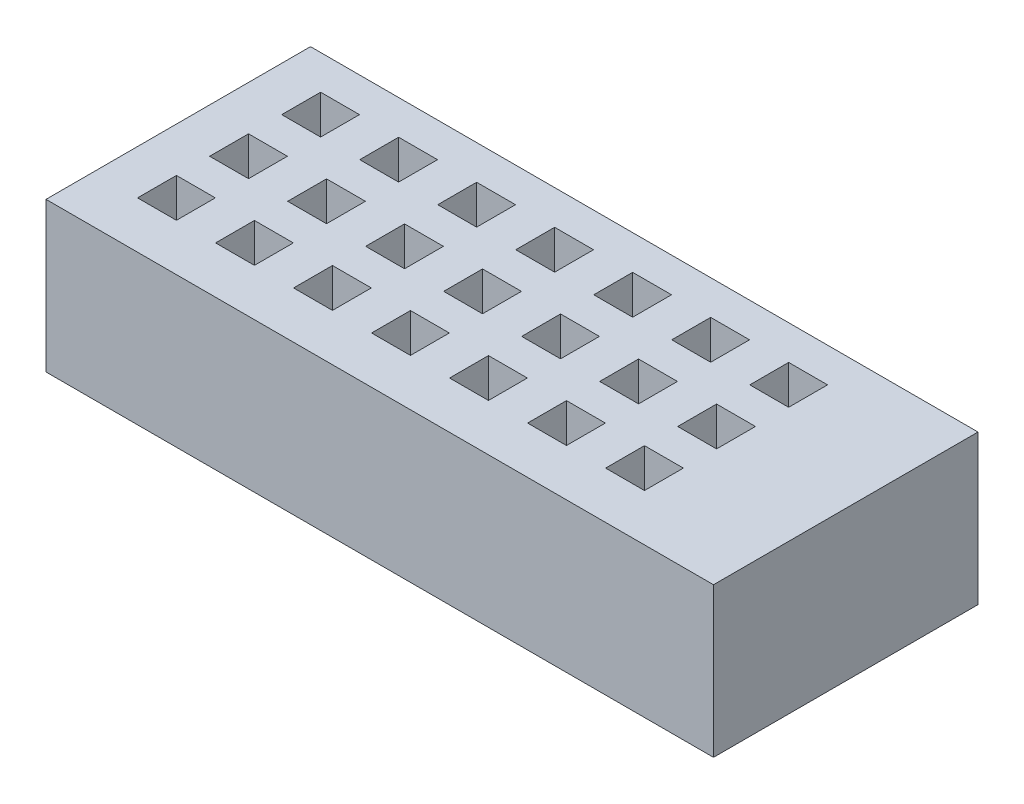
SolidWorks part; units mm, degrees
ref_plane "Front Plane" through (0, 0, 0) normal (0, 0, 1) x (1, 0, 0)
ref_plane "Top Plane" through (0, 0, 0) normal (0, 1, 0) x (1, 0, 0)
ref_plane "Right Plane" through (0, 0, 0) normal (1, 0, 0) x (0, 0, -1)
sketch "Sketch2" plane through (0, 8.128, 0) normal (0, -1, 0) x (1, 0, 0)
  line L4 (0, -10.7442) -> (-3.302, -10.7442) construction
  line L5 (-3.302, 4.064) -> (44.323, 4.064)
  line L6 (-3.302, 4.064) -> (-3.302, -14.8082)
  line L7 (-3.302, -14.8082) -> (44.323, -14.8082)
  line L8 (3.429, -0.8382) -> (3.429, 0.254)
  line L9 (3.429, 0.254) -> (-0.254, 0.254)
  line L10 (-0.254, 0.254) -> (-0.254, -0.8382)
  line L11 (-0.254, -0.8382) -> (3.429, -0.8382)
  line L12 (3.429, -0.8382) -> (3.429, 0.254)
  line L13 (3.429, 0.254) -> (-0.254, 0.254)
  line L14 (-0.254, 0.254) -> (-0.254, -0.8382)
  line L15 (-0.254, -0.8382) -> (3.429, -0.8382)
  line L16 (44.323, 4.064) -> (44.323, -14.8082)
  line L17 (0, 0) -> (0, 4.064) construction
  line L18 (41.783, 0) -> (44.323, 0) construction
  line L19 (41.783, -10.7442) -> (41.783, -14.8082) construction
  line L20 (5.2614, -0.8382) -> (8.9444, -0.8382)
  line L21 (8.9444, -0.8382) -> (8.9444, 0.254)
  line L22 (8.9444, 0.254) -> (5.2614, 0.254)
  line L23 (5.2614, 0.254) -> (5.2614, -0.8382)
  line L24 (10.7769, -0.8382) -> (14.4599, -0.8382)
  line L25 (14.4599, -0.8382) -> (14.4599, 0.254)
  line L26 (14.4599, 0.254) -> (10.7769, 0.254)
  line L27 (10.7769, 0.254) -> (10.7769, -0.8382)
  line L28 (16.2923, -0.8382) -> (19.9753, -0.8382)
  line L29 (19.9753, -0.8382) -> (19.9753, 0.254)
  line L30 (19.9753, 0.254) -> (16.2923, 0.254)
  line L31 (16.2923, 0.254) -> (16.2923, -0.8382)
  line L32 (21.8077, -0.8382) -> (25.4907, -0.8382)
  line L33 (25.4907, -0.8382) -> (25.4907, 0.254)
  line L34 (25.4907, 0.254) -> (21.8077, 0.254)
  line L35 (21.8077, 0.254) -> (21.8077, -0.8382)
  line L36 (27.3231, -0.8382) -> (31.0061, -0.8382)
  line L37 (31.0061, -0.8382) -> (31.0061, 0.254)
  line L38 (31.0061, 0.254) -> (27.3231, 0.254)
  line L39 (27.3231, 0.254) -> (27.3231, -0.8382)
  line L40 (32.8386, -0.8382) -> (36.5216, -0.8382)
  line L41 (36.5216, -0.8382) -> (36.5216, 0.254)
  line L42 (36.5216, 0.254) -> (32.8386, 0.254)
  line L43 (32.8386, 0.254) -> (32.8386, -0.8382)
  line L44 (38.354, -0.8382) -> (42.037, -0.8382)
  line L45 (42.037, -0.8382) -> (42.037, 0.254)
  line L46 (42.037, 0.254) -> (38.354, 0.254)
  line L47 (38.354, 0.254) -> (38.354, -0.8382)
  line L48 (5.2614, -5.9182) -> (8.9444, -5.9182)
  line L49 (8.9444, -5.9182) -> (8.9444, -4.826)
  line L50 (8.9444, -4.826) -> (5.2614, -4.826)
  line L51 (5.2614, -4.826) -> (5.2614, -5.9182)
  line L52 (10.7769, -5.9182) -> (14.4599, -5.9182)
  line L53 (14.4599, -5.9182) -> (14.4599, -4.826)
  line L54 (14.4599, -4.826) -> (10.7769, -4.826)
  line L55 (10.7769, -4.826) -> (10.7769, -5.9182)
  line L56 (16.2923, -5.9182) -> (19.9753, -5.9182)
  line L57 (19.9753, -5.9182) -> (19.9753, -4.826)
  line L58 (19.9753, -4.826) -> (16.2923, -4.826)
  line L59 (16.2923, -4.826) -> (16.2923, -5.9182)
  line L60 (21.8077, -5.9182) -> (25.4907, -5.9182)
  line L61 (25.4907, -5.9182) -> (25.4907, -4.826)
  line L62 (25.4907, -4.826) -> (21.8077, -4.826)
  line L63 (21.8077, -4.826) -> (21.8077, -5.9182)
  line L64 (27.3231, -5.9182) -> (31.0061, -5.9182)
  line L65 (31.0061, -5.9182) -> (31.0061, -4.826)
  line L66 (31.0061, -4.826) -> (27.3231, -4.826)
  line L67 (27.3231, -4.826) -> (27.3231, -5.9182)
  line L68 (32.8386, -5.9182) -> (36.5216, -5.9182)
  line L69 (36.5216, -5.9182) -> (36.5216, -4.826)
  line L70 (36.5216, -4.826) -> (32.8386, -4.826)
  line L71 (32.8386, -4.826) -> (32.8386, -5.9182)
  line L72 (38.354, -5.9182) -> (42.037, -5.9182)
  line L73 (42.037, -5.9182) -> (42.037, -4.826)
  line L74 (42.037, -4.826) -> (38.354, -4.826)
  line L75 (38.354, -4.826) -> (38.354, -5.9182)
  line L76 (5.2614, -10.9982) -> (8.9444, -10.9982)
  line L77 (8.9444, -10.9982) -> (8.9444, -9.906)
  line L78 (8.9444, -9.906) -> (5.2614, -9.906)
  line L79 (5.2614, -9.906) -> (5.2614, -10.9982)
  line L80 (10.7769, -10.9982) -> (14.4599, -10.9982)
  line L81 (14.4599, -10.9982) -> (14.4599, -9.906)
  line L82 (14.4599, -9.906) -> (10.7769, -9.906)
  line L83 (10.7769, -9.906) -> (10.7769, -10.9982)
  line L84 (16.2923, -10.9982) -> (19.9753, -10.9982)
  line L85 (19.9753, -10.9982) -> (19.9753, -9.906)
  line L86 (19.9753, -9.906) -> (16.2923, -9.906)
  line L87 (16.2923, -9.906) -> (16.2923, -10.9982)
  line L88 (21.8077, -10.9982) -> (25.4907, -10.9982)
  line L89 (25.4907, -10.9982) -> (25.4907, -9.906)
  line L90 (25.4907, -9.906) -> (21.8077, -9.906)
  line L91 (21.8077, -9.906) -> (21.8077, -10.9982)
  line L92 (27.3231, -10.9982) -> (31.0061, -10.9982)
  line L93 (31.0061, -10.9982) -> (31.0061, -9.906)
  line L94 (31.0061, -9.906) -> (27.3231, -9.906)
  line L95 (27.3231, -9.906) -> (27.3231, -10.9982)
  line L96 (32.8386, -10.9982) -> (36.5216, -10.9982)
  line L97 (36.5216, -10.9982) -> (36.5216, -9.906)
  line L98 (36.5216, -9.906) -> (32.8386, -9.906)
  line L99 (32.8386, -9.906) -> (32.8386, -10.9982)
  line L100 (38.354, -10.9982) -> (42.037, -10.9982)
  line L101 (42.037, -10.9982) -> (42.037, -9.906)
  line L102 (42.037, -9.906) -> (38.354, -9.906)
  line L103 (38.354, -9.906) -> (38.354, -10.9982)
  line L104 (-0.254, -5.9182) -> (3.429, -5.9182)
  line L105 (3.429, -5.9182) -> (3.429, -4.826)
  line L106 (3.429, -4.826) -> (-0.254, -4.826)
  line L107 (-0.254, -4.826) -> (-0.254, -5.9182)
  line L108 (-0.254, -10.9982) -> (3.429, -10.9982)
  line L109 (3.429, -10.9982) -> (3.429, -9.906)
  line L110 (3.429, -9.906) -> (-0.254, -9.906)
  line L111 (-0.254, -9.906) -> (-0.254, -10.9982)
  line L112 (0, -0.5842) -> (-0.254, -0.5842) construction
  line L113 (41.783, -0.5842) -> (42.037, -0.5842) construction
  dimension "D2" = 4.064
  dimension "D5" = 5.08
  dimension "D6" = 3.302
  dimension "D7" = 4.064
  dimension "D8" = 2.54
  dimension "D1" = 0.254
  dimension "D3" = 8
  dimension "D4" = 3
extrude "Boss-Extrude2" add sketch "Sketch2" along normal offset from surface (6.858 mm away) 1.27
sketch "Sketch4" plane through (0, 8.128, 0) normal (0, 1, 0) x (1, 0, 0)
  circle A1 centre (1.26, 0.6802) radius 0.731
  circle A2 centre (1.26, 0.6802) radius 0.35 construction
  circle A3 centre (6.8258, 0.6802) radius 0.731
  circle A4 centre (12.3915, 0.6802) radius 0.731
  circle A5 centre (17.9573, 0.6802) radius 0.731
  circle A6 centre (23.5231, 0.6802) radius 0.731
  circle A7 centre (29.0888, 0.6802) radius 0.731
  circle A8 centre (34.6546, 0.6802) radius 0.731
  circle A9 centre (40.2204, 0.6802) radius 0.731
  circle A10 centre (6.8258, 5.7602) radius 0.731
  circle A11 centre (12.3915, 5.7602) radius 0.731
  circle A12 centre (17.9573, 5.7602) radius 0.731
  circle A13 centre (23.5231, 5.7602) radius 0.731
  circle A14 centre (29.0888, 5.7602) radius 0.731
  circle A15 centre (34.6546, 5.7602) radius 0.731
  circle A16 centre (40.2204, 5.7602) radius 0.731
  circle A24 centre (1.26, 5.7602) radius 0.731
  circle A26 centre (1.26, 10.8402) radius 0.731
  circle A27 centre (6.8258, 10.8402) radius 0.731
  circle A28 centre (12.3915, 10.8402) radius 0.731
  circle A29 centre (17.9573, 10.8402) radius 0.731
  circle A30 centre (23.5231, 10.8402) radius 0.731
  circle A31 centre (29.0888, 10.8402) radius 0.731
  circle A32 centre (34.6546, 10.8402) radius 0.731
  circle A33 centre (40.2204, 10.8402) radius 0.731
  dimension "D1" = 0.381
  dimension "D4" = 5.08
  dimension "D2" = 8
  dimension "D3" = 3
extrude "Cut-Extrude1" cut sketch "Sketch4" against normal through all
sketch "Sketch5" plane through (0, 8.128, 0) normal (0, 1, 0) x (1, 0, 0)
  line L0 (44.323, -4.064) -> (-3.302, -4.064) construction
  line L1 (44.323, 14.8082) -> (44.323, -4.064) construction
  line L2 (-3.302, 14.8082) -> (44.323, 14.8082) construction
  line L3 (-3.302, -4.064) -> (-3.302, 14.8082) construction
  line L4 (44.323, -4.064) -> (-3.302, -4.064)
  line L5 (44.323, 14.8082) -> (44.323, -4.064)
  line L6 (-3.302, 14.8082) -> (44.323, 14.8082)
  line L7 (-3.302, -4.064) -> (-3.302, 14.8082)
  line L8 (5.4388, 2.0672) -> (5.4388, -0.7068)
  line L9 (8.2128, 2.0672) -> (5.4388, 2.0672)
  line L10 (8.2128, -0.7068) -> (8.2128, 2.0672)
  line L11 (5.4388, -0.7068) -> (8.2128, -0.7068)
  line L12 (11.0045, 2.0672) -> (11.0045, -0.7068)
  line L13 (13.7785, 2.0672) -> (11.0045, 2.0672)
  line L14 (13.7785, -0.7068) -> (13.7785, 2.0672)
  line L15 (11.0045, -0.7068) -> (13.7785, -0.7068)
  line L16 (-0.127, -0.7068) -> (2.647, -0.7068)
  line L17 (2.647, -0.7068) -> (2.647, 2.0672)
  line L18 (2.647, 2.0672) -> (-0.127, 2.0672)
  line L19 (-0.127, 2.0672) -> (-0.127, -0.7068)
  line L20 (-0.127, -0.7068) -> (2.647, -0.7068)
  line L21 (2.647, -0.7068) -> (2.647, 2.0672)
  line L22 (2.647, 2.0672) -> (-0.127, 2.0672)
  line L23 (-0.127, 2.0672) -> (-0.127, -0.7068)
  line L24 (16.5703, 2.0672) -> (16.5703, -0.7068)
  line L25 (19.3443, 2.0672) -> (16.5703, 2.0672)
  line L26 (19.3443, -0.7068) -> (19.3443, 2.0672)
  line L27 (16.5703, -0.7068) -> (19.3443, -0.7068)
  line L28 (22.1361, 2.0672) -> (22.1361, -0.7068)
  line L29 (24.9101, 2.0672) -> (22.1361, 2.0672)
  line L30 (24.9101, -0.7068) -> (24.9101, 2.0672)
  line L31 (22.1361, -0.7068) -> (24.9101, -0.7068)
  line L32 (27.7018, 2.0672) -> (27.7018, -0.7068)
  line L33 (30.4758, 2.0672) -> (27.7018, 2.0672)
  line L34 (30.4758, -0.7068) -> (30.4758, 2.0672)
  line L35 (27.7018, -0.7068) -> (30.4758, -0.7068)
  line L36 (33.2676, 2.0672) -> (33.2676, -0.7068)
  line L37 (36.0416, 2.0672) -> (33.2676, 2.0672)
  line L38 (36.0416, -0.7068) -> (36.0416, 2.0672)
  line L39 (33.2676, -0.7068) -> (36.0416, -0.7068)
  line L40 (38.8334, 2.0672) -> (38.8334, -0.7068)
  line L41 (41.6074, 2.0672) -> (38.8334, 2.0672)
  line L42 (41.6074, -0.7068) -> (41.6074, 2.0672)
  line L43 (38.8334, -0.7068) -> (41.6074, -0.7068)
  line L44 (5.4388, 7.2107) -> (5.4388, 4.4367)
  line L45 (8.2128, 7.2107) -> (5.4388, 7.2107)
  line L46 (8.2128, 4.4367) -> (8.2128, 7.2107)
  line L47 (5.4388, 4.4367) -> (8.2128, 4.4367)
  line L48 (11.0045, 7.2107) -> (11.0045, 4.4367)
  line L49 (13.7785, 7.2107) -> (11.0045, 7.2107)
  line L50 (13.7785, 4.4367) -> (13.7785, 7.2107)
  line L51 (11.0045, 4.4367) -> (13.7785, 4.4367)
  line L52 (16.5703, 7.2107) -> (16.5703, 4.4367)
  line L53 (19.3443, 7.2107) -> (16.5703, 7.2107)
  line L54 (19.3443, 4.4367) -> (19.3443, 7.2107)
  line L55 (16.5703, 4.4367) -> (19.3443, 4.4367)
  line L56 (22.1361, 7.2107) -> (22.1361, 4.4367)
  line L57 (24.9101, 7.2107) -> (22.1361, 7.2107)
  line L58 (24.9101, 4.4367) -> (24.9101, 7.2107)
  line L59 (22.1361, 4.4367) -> (24.9101, 4.4367)
  line L60 (27.7018, 7.2107) -> (27.7018, 4.4367)
  line L61 (30.4758, 7.2107) -> (27.7018, 7.2107)
  line L62 (30.4758, 4.4367) -> (30.4758, 7.2107)
  line L63 (27.7018, 4.4367) -> (30.4758, 4.4367)
  line L64 (33.2676, 7.2107) -> (33.2676, 4.4367)
  line L65 (36.0416, 7.2107) -> (33.2676, 7.2107)
  line L66 (36.0416, 4.4367) -> (36.0416, 7.2107)
  line L67 (33.2676, 4.4367) -> (36.0416, 4.4367)
  line L68 (38.8334, 7.2107) -> (38.8334, 4.4367)
  line L69 (41.6074, 7.2107) -> (38.8334, 7.2107)
  line L70 (41.6074, 4.4367) -> (41.6074, 7.2107)
  line L71 (38.8334, 4.4367) -> (41.6074, 4.4367)
  line L72 (-0.127, 7.2107) -> (-0.127, 4.4367)
  line L73 (2.647, 7.2107) -> (-0.127, 7.2107)
  line L74 (2.647, 4.4367) -> (2.647, 7.2107)
  line L75 (-0.127, 4.4367) -> (2.647, 4.4367)
  line L76 (-0.127, 12.3542) -> (-0.127, 9.5802)
  line L77 (2.647, 12.3542) -> (-0.127, 12.3542)
  line L78 (2.647, 9.5802) -> (2.647, 12.3542)
  line L79 (-0.127, 9.5802) -> (2.647, 9.5802)
  line L80 (5.4388, 12.3542) -> (5.4388, 9.5802)
  line L81 (8.2128, 12.3542) -> (5.4388, 12.3542)
  line L82 (8.2128, 9.5802) -> (8.2128, 12.3542)
  line L83 (5.4388, 9.5802) -> (8.2128, 9.5802)
  line L84 (11.0045, 12.3542) -> (11.0045, 9.5802)
  line L85 (13.7785, 12.3542) -> (11.0045, 12.3542)
  line L86 (13.7785, 9.5802) -> (13.7785, 12.3542)
  line L87 (11.0045, 9.5802) -> (13.7785, 9.5802)
  line L88 (16.5703, 12.3542) -> (16.5703, 9.5802)
  line L89 (19.3443, 12.3542) -> (16.5703, 12.3542)
  line L90 (19.3443, 9.5802) -> (19.3443, 12.3542)
  line L91 (16.5703, 9.5802) -> (19.3443, 9.5802)
  line L92 (22.1361, 12.3542) -> (22.1361, 9.5802)
  line L93 (24.9101, 12.3542) -> (22.1361, 12.3542)
  line L94 (24.9101, 9.5802) -> (24.9101, 12.3542)
  line L95 (22.1361, 9.5802) -> (24.9101, 9.5802)
  line L96 (27.7018, 12.3542) -> (27.7018, 9.5802)
  line L97 (30.4758, 12.3542) -> (27.7018, 12.3542)
  line L98 (30.4758, 9.5802) -> (30.4758, 12.3542)
  line L99 (27.7018, 9.5802) -> (30.4758, 9.5802)
  line L100 (33.2676, 12.3542) -> (33.2676, 9.5802)
  line L101 (36.0416, 12.3542) -> (33.2676, 12.3542)
  line L102 (36.0416, 9.5802) -> (36.0416, 12.3542)
  line L103 (33.2676, 9.5802) -> (36.0416, 9.5802)
  line L104 (38.8334, 12.3542) -> (38.8334, 9.5802)
  line L105 (41.6074, 12.3542) -> (38.8334, 12.3542)
  line L106 (41.6074, 9.5802) -> (41.6074, 12.3542)
  line L107 (38.8334, 9.5802) -> (41.6074, 9.5802)
  circle A0 centre (40.2204, 0.6802) radius 0.477 construction
  point P73 (40.2204, -0.7068)
  dimension "D1" = 0.127
  dimension "D2" = 8
  dimension "D3" = 3
extrude "Boss-Extrude3" add sketch "Sketch5" along normal blind 3.81
sketch "Sketch6" plane through (0, 8.128, 0) normal (0, 1, 0) x (1, 0, 0)
  line L0 (44.323, 14.8082) -> (-3.302, 14.8082) construction
  line L1 (38.0879, 14.8082) -> (42.9008, 14.8082)
  line L2 (38.0879, 14.8082) -> (38.0879, -4.064)
  line L3 (38.0879, -4.064) -> (42.9008, -4.064)
  line L4 (42.9008, 14.8082) -> (42.9008, -4.064)
  line L9 (-3.302, -4.064) -> (44.323, -4.064) construction
extrude "Boss-Extrude4" add sketch "Sketch6" along normal up to surface (3.81 mm away) up to face at (34.6546, 11.938, -10.9672)
